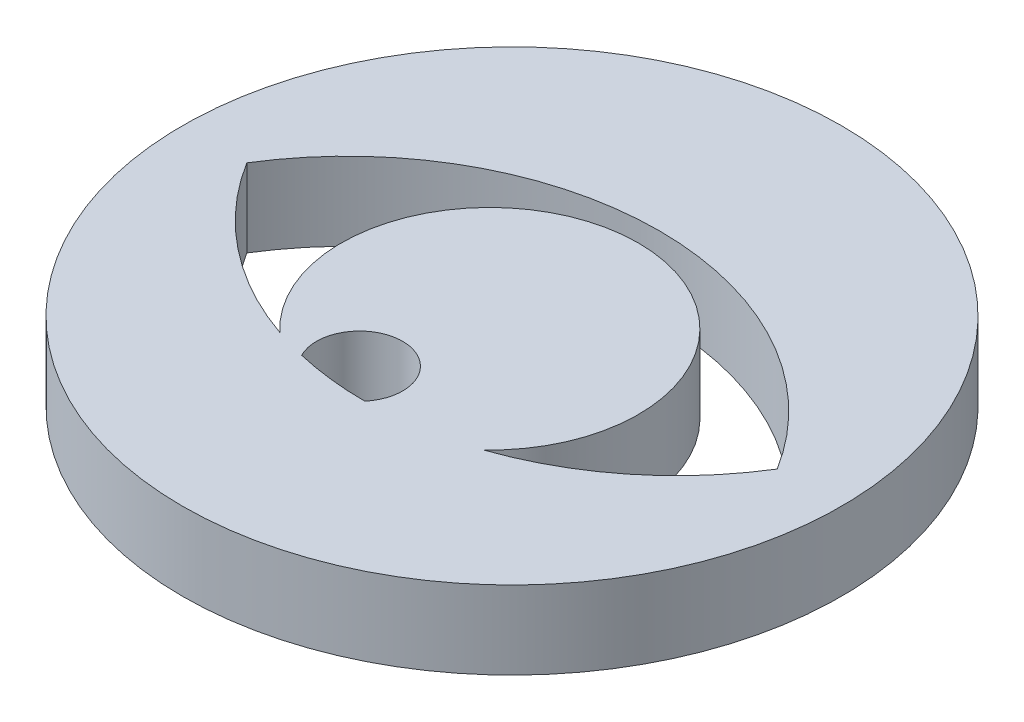
SolidWorks part; units mm, degrees
ref_plane "Front Plane" through (0, 0, 0) normal (0, 0, 1) x (1, 0, 0)
ref_plane "Top Plane" through (0, 0, 0) normal (0, 1, 0) x (1, 0, 0)
ref_plane "Right Plane" through (0, 0, 0) normal (1, 0, 0) x (0, 0, -1)
sketch "Sketch1" plane through (0, 0, 0) normal (0, 1, 0) x (1, 0, 0)
  circle A0 centre (0, 0) radius 9.5
  arc A1 (2.9345, -3.7582) -> (-2.9345, -3.7582) centre (0, -0.639) ccw
  arc A2 (-7.6444, 0) -> (-2.9345, -3.7582) centre (0, 4.75) ccw
  arc A3 (7.6444, 0) -> (-7.6444, 0) centre (0, -4.75) ccw
  arc A4 (0, -4.2578) -> (-2.0501, -4.0134) centre (-0.9433, -3.4505) ccw
  arc A5 (-2.0501, -4.0134) -> (0.0066, -4.25) centre (0, 4.75) ccw
  arc A6 (2.9345, -3.7582) -> (7.6444, 0) centre (0, 4.75) ccw
  dimension "D1" = 19
  dimension "D2" = 4.2826
  dimension "D3" = 9
  dimension "D4" = 1.2416
  dimension "D5" = 0.0066
  dimension "D6" = 2.9345
  dimension "D7" = 7.6444
  dimension "D8" = 0.9433
extrude "Boss-Extrude1" add sketch "Sketch1" along normal blind 2.25
